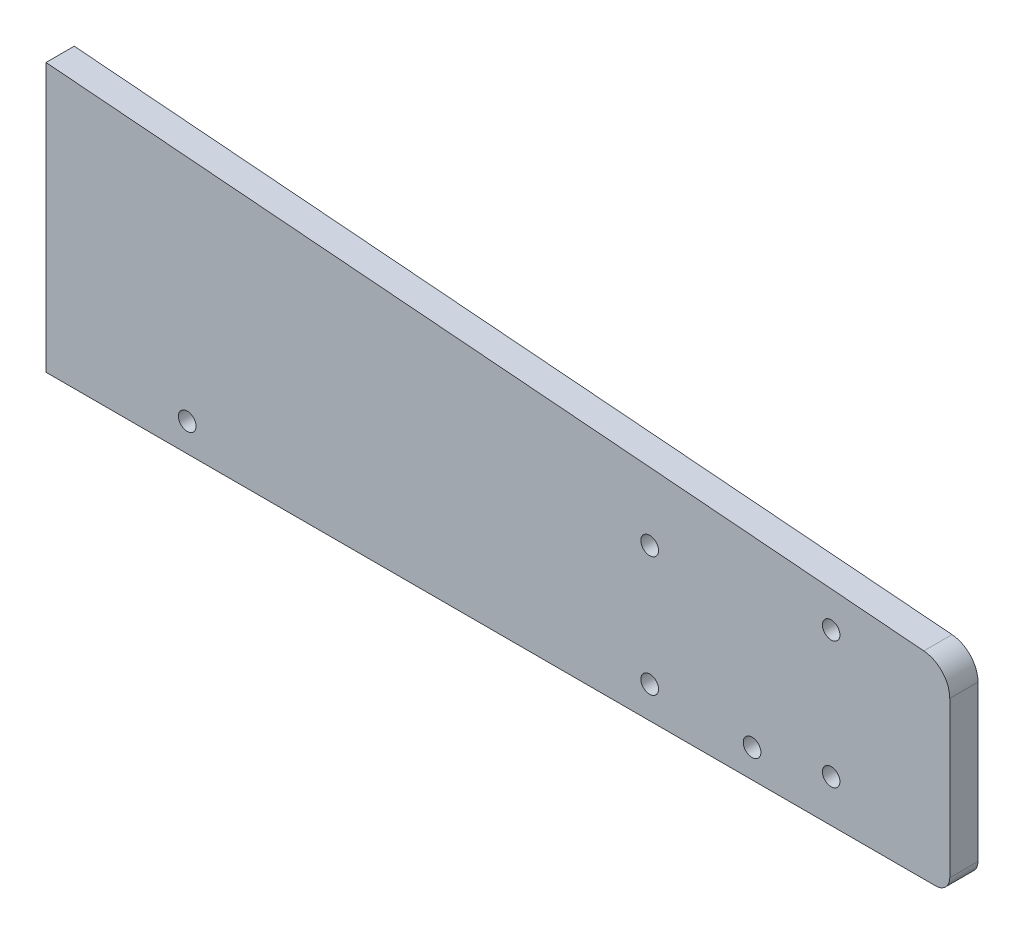
SolidWorks part; units mm, degrees
material "PE High Density"
ref_plane "Front Plane" through (0, 0, 0) normal (0, 0, 1) x (1, 0, 0)
ref_plane "Top Plane" through (0, 0, 0) normal (0, 1, 0) x (1, 0, 0)
ref_plane "Right Plane" through (0, 0, 0) normal (1, 0, 0) x (0, 0, -1)
sketch "Sketch1" plane through (0, 0, 0) normal (0, 0, 1) x (1, 0, 0)
  line L0 (63.5, 0) -> (63.5, 120.65)
  line L1 (0, 0) -> (1219.2, 0) construction
  line L2 (0, 0) -> (0, 1778) construction
  line L3 (0, 1778) -> (1219.2, 1778) construction
  line L4 (1219.2, 0) -> (1219.2, 1778) construction
  line L5 (63.5, 120.65) -> (458.2196, 88.859)
  line L6 (469.9, 76.2) -> (469.9, 0)
  line L7 (469.9, 0) -> (63.5, 0)
  circle A0 centre (609.6, 241.3) radius 241.3 construction
  arc A1 (469.9, 76.2) -> (458.2196, 88.859) centre (457.2, 76.2) ccw
  dimension "D3" = 609.6
  dimension "D4" = 482.6
  dimension "D10" = 12.7
  dimension "D1" = 1219.2
  dimension "D2" = 1778
  dimension "D5" = 241.3
  dimension "D6" = 63.5
  dimension "D7" = 406.4
  dimension "D8" = 76.2
  dimension "D9" = 120.65
  dimension "D11" = 4.605
extrude "Boss-Extrude1" add sketch "Sketch1" along normal blind 12.7
sketch "Sketch2" plane through (0, 0, 12.7) normal (0, 0, 1) x (1, 0, 0)
  line L0 (63.5, 0) -> (469.9, 0) construction
  line L1 (63.5, 120.65) -> (63.5, 0) construction
  circle A0 centre (127, 12.7) radius 3.9687
  circle A1 centre (381, 12.7) radius 3.9688
  dimension "D1" = 12.7
  dimension "D4" = 7.9375
  dimension "D2" = 63.5
  dimension "D3" = 254
extrude "Cut-Extrude1" cut sketch "Sketch2" against normal through all
fillet "Fillet1" radius 6.35 1 edges at (469.9, 0, 6.35)
sketch "Sketch4" plane through (0, 0, 0) normal (0, 0, -1) x (-1, 0, 0)
  line L0 (-469.9, 6.35) -> (-469.9, 76.2) construction
  line L1 (-63.5, 0) -> (-463.55, 0) construction
  circle A0 centre (-416.5676, 76.2) radius 3.937
  circle A1 centre (-416.5676, 19.05) radius 3.937
  dimension "D4" = 7.874
  dimension "D1" = 57.15
  dimension "D2" = 53.3324
  dimension "D3" = 19.05
extrude "Cut-Extrude2" cut sketch "Sketch4" against normal through all
hole_wizard "5/16 (0.3125) Diameter Hole1" positions "Sketch5" profile "Sketch6" hole size "5/16" standard "ANSI Inch" end condition through all
sketch "Sketch5" plane through (0, 0, 12.7) normal (0, 0, 1) x (1, 0, 0)
  line L0 (63.5, 0) -> (463.55, 0) construction
  line L1 (63.5, 120.65) -> (63.5, 0) construction
  point P0 (334.9625, 14.2875)
  point P2 (334.9625, 68.2625)
  dimension "D1" = 53.975
  dimension "D2" = 14.2875
  dimension "D3" = 271.4625
sketch "Sketch6" plane through (334.9625, 14.2875, 12.7) normal (1, 0, 0) x (0, -1, 0)
  line L0 (0, 0) -> (0, 12.7)
  line L1 (0, 12.7) -> (3.9687, 12.7)
  line L2 (3.9687, 12.7) -> (3.9687, 0)
  line L5 (3.9687, 0) -> (0, 0)
  line L11 (0, -6.35) -> (0, 107.95) construction
  dimension "Thru Hole Dia." = 7.9375
  dimension "Thru Hole Depth" = 12.7
